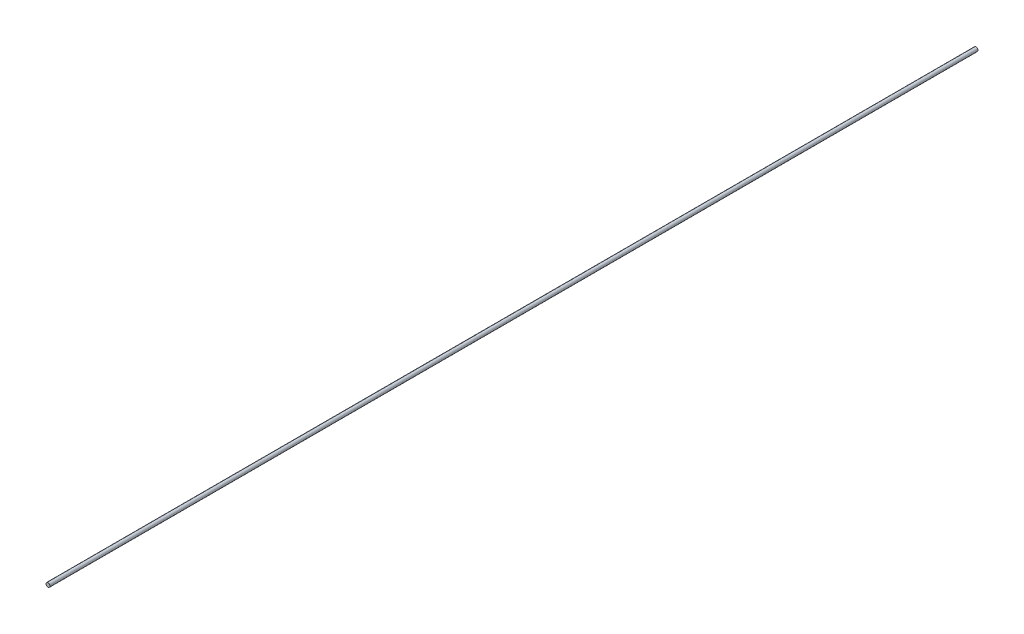
SolidWorks part; units mm, degrees
ref_plane "Front Plane" through (0, 0, 0) normal (0, 0, 1) x (1, 0, 0)
ref_plane "Top Plane" through (0, 0, 0) normal (0, 1, 0) x (1, 0, 0)
ref_plane "Right Plane" through (0, 0, 0) normal (1, 0, 0) x (0, 0, -1)
sketch "Sketch1" plane through (0, 0, 0) normal (0, 0, 1) x (1, 0, 0)
  circle A0 centre (0, 0) radius 1.55
  dimension "D1" = 3.1
extrude "Boss-Extrude1" add sketch "Sketch1" along normal mid plane 720
